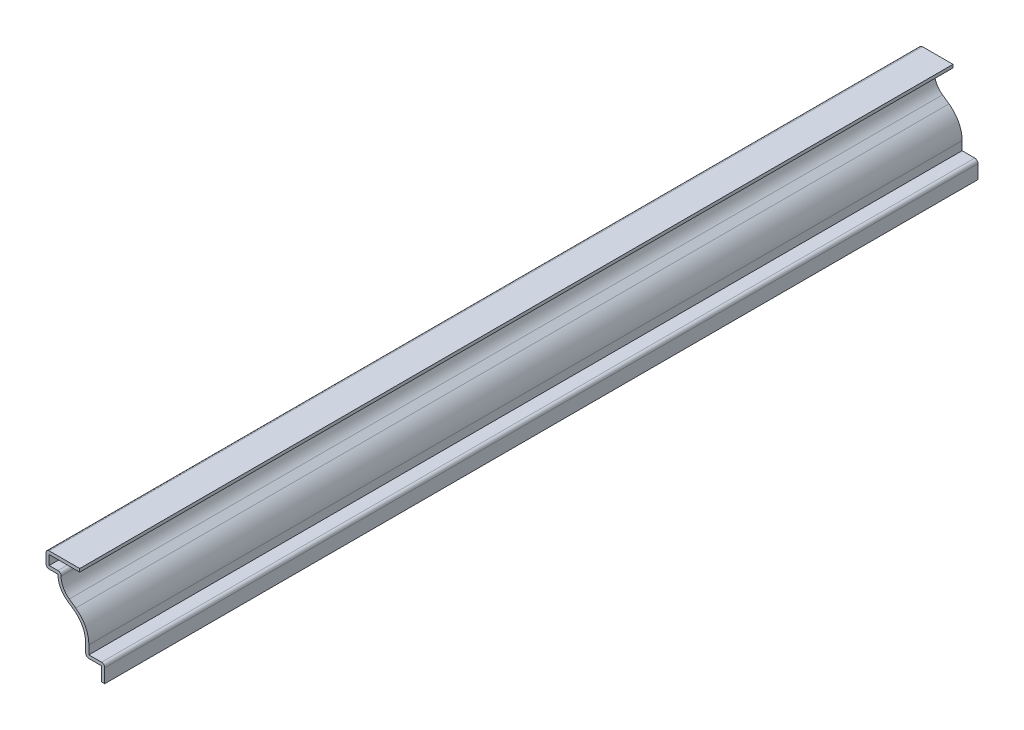
SolidWorks part; units mm, degrees
ref_plane "Front Plane" through (0, 0, 0) normal (0, 0, 1) x (1, 0, 0)
ref_plane "Top Plane" through (0, 0, 0) normal (0, 1, 0) x (1, 0, 0)
ref_plane "Right Plane" through (0, 0, 0) normal (1, 0, 0) x (0, 0, -1)
sketch "Sketch1" plane through (0, 0, 0) normal (0, 0, 1) x (1, 0, 0)
  line L0 (0, 0) -> (0, 5.5562)
  line L1 (0, 5.5562) -> (-6.35, 5.5562)
  line L2 (-6.35, 5.5562) -> (-6.35, 10.3187)
  line L3 (-17.4625, 28.575) -> (-22.225, 28.575)
  line L4 (-22.225, 28.575) -> (-22.225, 34.925)
  line L5 (-22.225, 34.925) -> (-8.7312, 34.925)
  line L6 (-11.0593, 19.401) -> (-13.6542, 21.2305)
  arc A0 (-6.35, 10.3187) -> (-11.0593, 19.401) centre (-17.4625, 10.3187) ccw
  arc A1 (-13.6542, 21.2305) -> (-17.4625, 28.575) centre (-8.4761, 28.575) cw
  point P9 (0, 0)
  point P13 (-12.3883, 17.9867)
  point P14 (0, 0)
  point P15 (0, 0)
  point P16 (0, 0)
  point P18 (-9.847, 15.022)
  point P19 (-12.2672, 16.8976)
  point P20 (-6.35, 7.8218)
  point P21 (-12.9952, 18.3194)
  point P22 (-10.683, 19.1236)
  dimension "D8" = 4.7625
  dimension "D1" = 34.925
  dimension "D2" = 13.4937
  dimension "D3" = 6.35
  dimension "D4" = 23.0188
  dimension "D5" = 6.35
  dimension "D6" = 22.225
  dimension "D7" = 11.1125
  dimension "D9" = 3.175
extrude "Extrude-Thin1" add sketch "Sketch1" against normal blind 349.25 thin
fillet "Fillet1" radius 1.27 5 edges at (1.27, 6.8262, -174.625) (-6.35, 5.5562, -174.625) (-16.0873, 29.845, -174.625) (-22.225, 28.575, -174.625) (-22.225, 34.925, -174.625)
